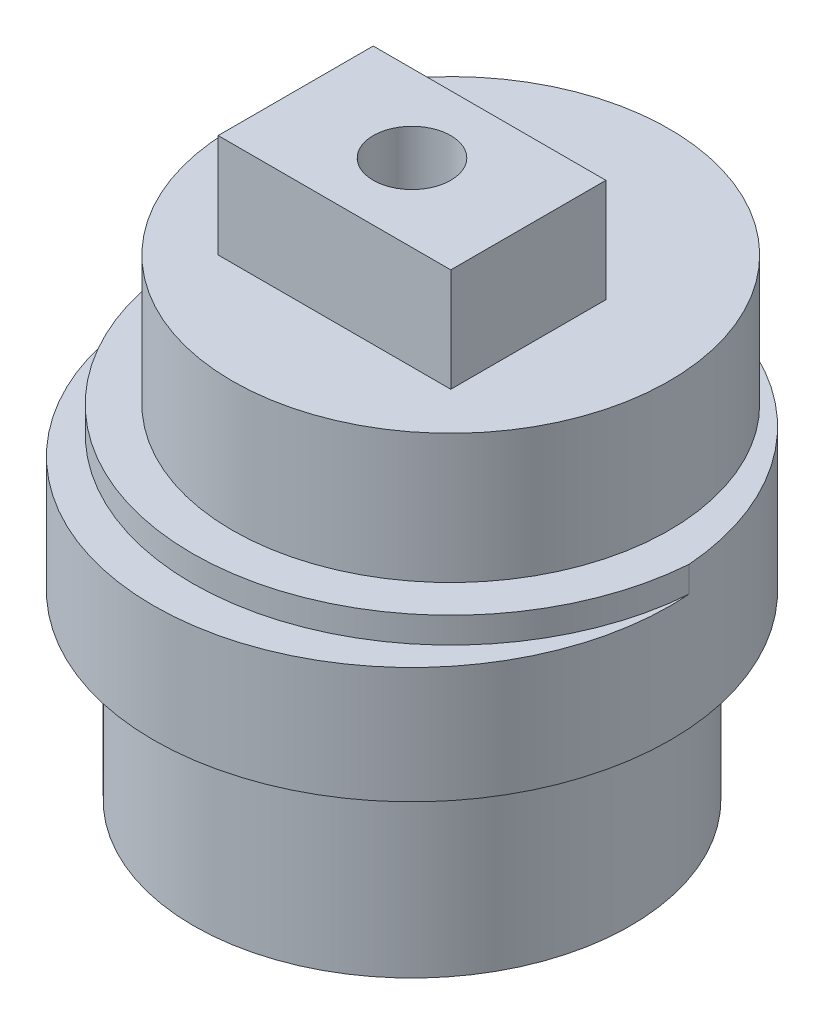
SolidWorks part; units mm, degrees
ref_plane "Front Plane" through (0, 0, 0) normal (0, 0, 1) x (1, 0, 0)
ref_plane "Top Plane" through (0, 0, 0) normal (0, 1, 0) x (1, 0, 0)
ref_plane "Right Plane" through (0, 0, 0) normal (1, 0, 0) x (0, 0, -1)
sketch "Sketch1" plane through (0, 0, 0) normal (0, 1, 0) x (1, 0, 0)
  circle A0 centre (0, 0) radius 8.45
  dimension "D1" = 16.9
extrude "Boss-Extrude1" add sketch "Sketch1" along normal blind 7
sketch "Sketch2" plane through (0, 7, 0) normal (0, 1, 0) x (1, 0, 0)
  circle A0 centre (0, 0) radius 10
  dimension "D1" = 20
extrude "Boss-Extrude2" add sketch "Sketch2" along normal blind 4.5
sketch "Sketch3" plane through (0, 11.5, 0) normal (0, 1, 0) x (1, 0, 0)
  circle A0 centre (0, 1.5) radius 8.45
  dimension "D1" = 16.9
  dimension "D2" = 1.5
extrude "Boss-Extrude3" add sketch "Sketch3" along normal blind 6
sketch "Sketch4" plane through (0, 11.5, 0) normal (0, 1, 0) x (1, 0, 0)
  circle A0 centre (0, 1.5) radius 8.45 construction
  circle A1 centre (0, 1.5) radius 8.45
  circle A2 centre (0, 0) radius 10 construction
  arc A3 (0, -10) -> (-9.9718, 0.75) centre (0, 0) ccw
  arc A4 (-9.9718, 0.75) -> (9.9718, 0.75) centre (0, 1.5) ccw
  arc A5 (9.9718, 0.75) -> (0, -10) centre (0, 0) ccw
  circle M1 centre (0, 1.5) radius 8.45
  circle M2 centre (0, 0) radius 10
  dimension "D1" = 20
extrude "Boss-Extrude4" add sketch "Sketch4" along normal blind 1 contours A4 M2 M1
sketch "Sketch5" plane through (0, 17.5, 0) normal (0, 1, 0) x (1, 0, 0)
  line L1 (-4.5, -3) -> (4.5, -3)
  line L2 (-4.5, -3) -> (-4.5, 3)
  line L3 (-4.5, 3) -> (4.5, 3)
  line L4 (4.5, -3) -> (4.5, 3)
  line L5 (-4.5, -3) -> (4.5, 3) construction
  line L6 (-4.5, 3) -> (4.5, -3) construction
  point P2 (0, 0)
  dimension "D3" = 9
  dimension "D4" = 6
extrude "Boss-Extrude5" add sketch "Sketch5" along normal blind 4
sketch "Sketch6" plane through (0, 21.5, 0) normal (0, 1, 0) x (1, 0, 0)
  circle A0 centre (0, 0) radius 1.5
  dimension "D1" = 3
extrude "Cut-Extrude1" cut sketch "Sketch6" against normal blind 8
sketch "Sketch7" plane through (0, 0, 0) normal (0, -1, 0) x (-1, 0, 0)
  circle A0 centre (0, -5.5) radius 1.5
  circle A1 centre (-5.5, 0) radius 1.5
  circle A2 centre (0, 5.5) radius 1.5
  circle A3 centre (5.5, 0) radius 1.5
  point P12 (0, 0)
  dimension "D3" = 3
  dimension "D1" = 5.5
  dimension "D2" = 4
extrude "Cut-Extrude2" [suppressed] cut sketch "Sketch7" against normal blind 8
sketch "Sketch8" plane through (0, 0, 0) normal (0, -1, 0) x (1, 0, 0)
  arc A0 (1.9433, 2.9259) -> (1.4435, 3.2021) centre (0, 0) ccw
  arc A1 (-2.4201, 2.5457) -> (-2.8006, 2.1199) centre (0, 0) ccw
  arc A2 (3.4992, 0.3049) -> (3.4036, 0.8679) centre (0, 0) ccw
  arc A3 (2.4201, -2.5457) -> (2.8006, -2.1199) centre (0, 0) ccw
  arc A4 (-1.0759, 3.3436) -> (-1.6035, 3.1251) centre (0, 0) ccw
  arc A5 (-3.0204, -1.793) -> (-2.6899, -2.2587) centre (0, 0) ccw
  arc A6 (0.4814, 3.4793) -> (-0.0888, 3.5113) centre (0, 0) ccw
  arc A7 (3.0204, 1.793) -> (2.6899, 2.2587) centre (0, 0) ccw
  arc A8 (3.285, -1.2435) -> (3.4431, -0.6948) centre (0, 0) ccw
  arc A9 (-3.285, 1.2435) -> (-3.4431, 0.6948) centre (0, 0) ccw
  arc A10 (1.0759, -3.3436) -> (1.6035, -3.1251) centre (0, 0) ccw
  arc A11 (-1.9433, -2.9259) -> (-1.4435, -3.2021) centre (0, 0) ccw
  arc A12 (-0.4814, -3.4793) -> (0.0888, -3.5113) centre (0, 0) ccw
  arc A13 (-3.4992, -0.3049) -> (-3.4036, -0.8679) centre (0, 0) ccw
  spline S0 degree 3 poles (-2.6899, -2.2587) (-2.6998, -2.278) (-2.7192, -2.3185) (-2.7467, -2.3829) (-2.7734, -2.4537) (-2.7988, -2.5314) (-2.8225, -2.6162) (-2.8438, -2.7079) (-2.8627, -2.8065) (-2.877, -2.9191) (-2.8909, -3.0073) (-2.8865, -3.0684) (-2.8815, -3.0926) (-2.874, -3.1162) (-2.8635, -3.1386) (-2.8488, -3.1646) (-2.8257, -3.1852) (-2.7982, -3.1969) (-2.7748, -3.2048) (-2.7506, -3.2097) (-2.7259, -3.2119) (-2.6647, -3.2094) (-2.5786, -3.1858) (-2.4684, -3.1589) (-2.3725, -3.1291) (-2.2837, -3.0977) (-2.2021, -3.0646) (-2.1277, -3.0307) (-2.0604, -2.9963) (-1.9994, -2.9617) (-1.9614, -2.9379) (-1.9433, -2.9259) knots 0.027203 0.027203 0.027203 0.027203 0.059318 0.093556 0.130845 0.171187 0.214581 0.261026 0.310525 0.363075 0.429245 0.441417 0.453589 0.465761 0.477933 0.490104 0.509896 0.522067 0.534239 0.546411 0.558583 0.570755 0.636925 0.689475 0.738974 0.785419 0.828813 0.869155 0.906444 0.940682 0.972797 0.972797 0.972797 0.972797 weights 1 1 1 1 1 1 1 1 1 1 1 1 1 1 1 1 1 1 1 1 1 1 1 1 1 1 1 1 1 1 1 1
  spline S1 degree 3 poles (-1.6035, 3.1251) (-1.6202, 3.139) (-1.6552, 3.1669) (-1.7119, 3.2081) (-1.775, 3.2498) (-1.8451, 3.2919) (-1.9225, 3.3339) (-2.0072, 3.3751) (-2.0992, 3.4154) (-2.2057, 3.4545) (-2.2886, 3.4876) (-2.3492, 3.4969) (-2.3739, 3.4975) (-2.3985, 3.4953) (-2.4227, 3.4901) (-2.4514, 3.4815) (-2.4765, 3.4637) (-2.4941, 3.4395) (-2.507, 3.4184) (-2.5172, 3.3958) (-2.5248, 3.3723) (-2.536, 3.312) (-2.5321, 3.2229) (-2.5304, 3.1094) (-2.5227, 3.0093) (-2.5119, 2.9157) (-2.4978, 2.8289) (-2.4812, 2.7487) (-2.4627, 2.6754) (-2.4425, 2.6083) (-2.4278, 2.566) (-2.4201, 2.5457) knots 0.027203 0.027203 0.027203 0.027203 0.059318 0.093556 0.130845 0.171187 0.214581 0.261026 0.310525 0.363075 0.429245 0.441417 0.453589 0.465761 0.477933 0.490104 0.509896 0.522067 0.534239 0.546411 0.558583 0.570755 0.636925 0.689475 0.738974 0.785419 0.828813 0.869155 0.906444 0.940682 0.972797 0.972797 0.972797 0.972797 weights 1 1 1 1 1 1 1 1 1 1 1 1 1 1 1 1 1 1 1 1 1 1 1 1 1 1 1 1 1 1 1 1
  spline S2 degree 3 poles (2.6899, 2.2587) (2.6998, 2.278) (2.7192, 2.3185) (2.7467, 2.3829) (2.7734, 2.4537) (2.7988, 2.5314) (2.8225, 2.6162) (2.8438, 2.7079) (2.8627, 2.8065) (2.877, 2.9191) (2.8909, 3.0073) (2.8865, 3.0684) (2.8815, 3.0926) (2.874, 3.1162) (2.8635, 3.1386) (2.8488, 3.1646) (2.8257, 3.1852) (2.7982, 3.1969) (2.7748, 3.2048) (2.7506, 3.2097) (2.7259, 3.2119) (2.6647, 3.2094) (2.5786, 3.1858) (2.4684, 3.1589) (2.3725, 3.1291) (2.2837, 3.0977) (2.2021, 3.0646) (2.1277, 3.0307) (2.0604, 2.9963) (1.9994, 2.9617) (1.9614, 2.9379) (1.9433, 2.9259) knots 0.027203 0.027203 0.027203 0.027203 0.059318 0.093556 0.130845 0.171187 0.214581 0.261026 0.310525 0.363075 0.429245 0.441417 0.453589 0.465761 0.477933 0.490104 0.509896 0.522067 0.534239 0.546411 0.558583 0.570755 0.636925 0.689475 0.738974 0.785419 0.828813 0.869155 0.906444 0.940682 0.972797 0.972797 0.972797 0.972797 weights 1 1 1 1 1 1 1 1 1 1 1 1 1 1 1 1 1 1 1 1 1 1 1 1 1 1 1 1 1 1 1 1
  spline S3 degree 3 poles (3.4036, 0.8679) (3.4208, 0.881) (3.4559, 0.909) (3.5086, 0.9551) (3.5633, 1.0074) (3.62, 1.0664) (3.6781, 1.1324) (3.7371, 1.2058) (3.7969, 1.2865) (3.8587, 1.3817) (3.9094, 1.4551) (3.9319, 1.5121) (3.938, 1.5361) (3.9414, 1.5606) (3.9417, 1.5853) (3.9397, 1.6152) (3.9279, 1.6437) (3.9082, 1.6662) (3.8905, 1.6835) (3.8708, 1.6984) (3.8495, 1.7111) (3.7933, 1.7354) (3.7055, 1.7515) (3.5945, 1.7751) (3.4952, 1.7899) (3.4016, 1.8001) (3.3137, 1.8057) (3.232, 1.8073) (3.1564, 1.8056) (3.0865, 1.8009) (3.0419, 1.7959) (3.0204, 1.793) knots 0.027203 0.027203 0.027203 0.027203 0.059318 0.093556 0.130845 0.171187 0.214581 0.261026 0.310525 0.363075 0.429245 0.441417 0.453589 0.465761 0.477933 0.490104 0.509896 0.522067 0.534239 0.546411 0.558583 0.570755 0.636925 0.689475 0.738974 0.785419 0.828813 0.869155 0.906444 0.940682 0.972797 0.972797 0.972797 0.972797 weights 1 1 1 1 1 1 1 1 1 1 1 1 1 1 1 1 1 1 1 1 1 1 1 1 1 1 1 1 1 1 1 1
  spline S4 degree 3 poles (2.8006, -2.1199) (2.8217, -2.1252) (2.8654, -2.1351) (2.9343, -2.1476) (3.0093, -2.1578) (3.0907, -2.1653) (3.1786, -2.1696) (3.2728, -2.1699) (3.3732, -2.1664) (3.4861, -2.1553) (3.5751, -2.1492) (3.6338, -2.1313) (3.6563, -2.1211) (3.6776, -2.1085) (3.6971, -2.0933) (3.7192, -2.0731) (3.7341, -2.0461) (3.7394, -2.0167) (3.7419, -1.9921) (3.7413, -1.9674) (3.7379, -1.9429) (3.7219, -1.8837) (3.6797, -1.8051) (3.629, -1.7036) (3.5786, -1.6167) (3.5282, -1.5371) (3.4778, -1.465) (3.4281, -1.4) (3.3796, -1.342) (3.3324, -1.2903) (3.3007, -1.2585) (3.285, -1.2435) knots 0.027203 0.027203 0.027203 0.027203 0.059318 0.093556 0.130845 0.171187 0.214581 0.261026 0.310525 0.363075 0.429245 0.441417 0.453589 0.465761 0.477933 0.490104 0.509896 0.522067 0.534239 0.546411 0.558583 0.570755 0.636925 0.689475 0.738974 0.785419 0.828813 0.869155 0.906444 0.940682 0.972797 0.972797 0.972797 0.972797 weights 1 1 1 1 1 1 1 1 1 1 1 1 1 1 1 1 1 1 1 1 1 1 1 1 1 1 1 1 1 1 1 1
  spline S5 degree 3 poles (-2.8006, 2.1199) (-2.8217, 2.1252) (-2.8654, 2.1351) (-2.9343, 2.1476) (-3.0093, 2.1578) (-3.0907, 2.1653) (-3.1786, 2.1696) (-3.2728, 2.1699) (-3.3732, 2.1664) (-3.4861, 2.1553) (-3.5751, 2.1492) (-3.6338, 2.1313) (-3.6563, 2.1211) (-3.6776, 2.1085) (-3.6971, 2.0933) (-3.7192, 2.0731) (-3.7341, 2.0461) (-3.7394, 2.0167) (-3.7419, 1.9921) (-3.7413, 1.9674) (-3.7379, 1.9429) (-3.7219, 1.8837) (-3.6797, 1.8051) (-3.629, 1.7036) (-3.5786, 1.6167) (-3.5282, 1.5371) (-3.4778, 1.465) (-3.4281, 1.4) (-3.3796, 1.342) (-3.3324, 1.2903) (-3.3007, 1.2585) (-3.285, 1.2435) knots 0.027203 0.027203 0.027203 0.027203 0.059318 0.093556 0.130845 0.171187 0.214581 0.261026 0.310525 0.363075 0.429245 0.441417 0.453589 0.465761 0.477933 0.490104 0.509896 0.522067 0.534239 0.546411 0.558583 0.570755 0.636925 0.689475 0.738974 0.785419 0.828813 0.869155 0.906444 0.940682 0.972797 0.972797 0.972797 0.972797 weights 1 1 1 1 1 1 1 1 1 1 1 1 1 1 1 1 1 1 1 1 1 1 1 1 1 1 1 1 1 1 1 1
  spline S6 degree 3 poles (1.4435, 3.2021) (1.444, 3.2238) (1.444, 3.2687) (1.4408, 3.3387) (1.4341, 3.414) (1.4233, 3.4951) (1.4079, 3.5817) (1.3873, 3.6736) (1.3615, 3.7707) (1.3256, 3.8783) (1.2998, 3.9638) (1.2693, 4.0169) (1.2543, 4.0366) (1.2373, 4.0546) (1.2182, 4.0702) (1.1936, 4.0872) (1.1639, 4.0958) (1.134, 4.0944) (1.1095, 4.0914) (1.0855, 4.0852) (1.0624, 4.0765) (1.0083, 4.0478) (0.941, 3.9891) (0.8533, 3.9171) (0.7798, 3.8486) (0.7135, 3.7818) (0.6543, 3.7166) (0.6021, 3.6537) (0.5563, 3.5935) (0.5164, 3.5359) (0.4925, 3.498) (0.4814, 3.4793) knots 0.027203 0.027203 0.027203 0.027203 0.059318 0.093556 0.130845 0.171187 0.214581 0.261026 0.310525 0.363075 0.429245 0.441417 0.453589 0.465761 0.477933 0.490104 0.509896 0.522067 0.534239 0.546411 0.558583 0.570755 0.636925 0.689475 0.738974 0.785419 0.828813 0.869155 0.906444 0.940682 0.972797 0.972797 0.972797 0.972797 weights 1 1 1 1 1 1 1 1 1 1 1 1 1 1 1 1 1 1 1 1 1 1 1 1 1 1 1 1 1 1 1 1
  spline S7 degree 3 poles (-1.4435, -3.2021) (-1.444, -3.2238) (-1.444, -3.2687) (-1.4408, -3.3387) (-1.4341, -3.414) (-1.4233, -3.4951) (-1.4079, -3.5817) (-1.3873, -3.6736) (-1.3615, -3.7707) (-1.3256, -3.8783) (-1.2998, -3.9638) (-1.2693, -4.0169) (-1.2543, -4.0366) (-1.2373, -4.0546) (-1.2182, -4.0702) (-1.1936, -4.0872) (-1.1639, -4.0958) (-1.134, -4.0944) (-1.1095, -4.0914) (-1.0855, -4.0852) (-1.0624, -4.0765) (-1.0083, -4.0478) (-0.941, -3.9891) (-0.8533, -3.9171) (-0.7798, -3.8486) (-0.7135, -3.7818) (-0.6543, -3.7166) (-0.6021, -3.6537) (-0.5563, -3.5935) (-0.5164, -3.5359) (-0.4925, -3.498) (-0.4814, -3.4793) knots 0.027203 0.027203 0.027203 0.027203 0.059318 0.093556 0.130845 0.171187 0.214581 0.261026 0.310525 0.363075 0.429245 0.441417 0.453589 0.465761 0.477933 0.490104 0.509896 0.522067 0.534239 0.546411 0.558583 0.570755 0.636925 0.689475 0.738974 0.785419 0.828813 0.869155 0.906444 0.940682 0.972797 0.972797 0.972797 0.972797 weights 1 1 1 1 1 1 1 1 1 1 1 1 1 1 1 1 1 1 1 1 1 1 1 1 1 1 1 1 1 1 1 1
  spline S8 degree 3 poles (-3.4036, -0.8679) (-3.4208, -0.881) (-3.4559, -0.909) (-3.5086, -0.9551) (-3.5633, -1.0074) (-3.62, -1.0664) (-3.6781, -1.1324) (-3.7371, -1.2058) (-3.7969, -1.2865) (-3.8587, -1.3817) (-3.9094, -1.4551) (-3.9319, -1.5121) (-3.938, -1.5361) (-3.9414, -1.5606) (-3.9417, -1.5853) (-3.9397, -1.6152) (-3.9279, -1.6437) (-3.9082, -1.6662) (-3.8905, -1.6835) (-3.8708, -1.6984) (-3.8495, -1.7111) (-3.7933, -1.7354) (-3.7055, -1.7515) (-3.5945, -1.7751) (-3.4952, -1.7899) (-3.4016, -1.8001) (-3.3137, -1.8057) (-3.232, -1.8073) (-3.1564, -1.8056) (-3.0865, -1.8009) (-3.0419, -1.7959) (-3.0204, -1.793) knots 0.027203 0.027203 0.027203 0.027203 0.059318 0.093556 0.130845 0.171187 0.214581 0.261026 0.310525 0.363075 0.429245 0.441417 0.453589 0.465761 0.477933 0.490104 0.509896 0.522067 0.534239 0.546411 0.558583 0.570755 0.636925 0.689475 0.738974 0.785419 0.828813 0.869155 0.906444 0.940682 0.972797 0.972797 0.972797 0.972797 weights 1 1 1 1 1 1 1 1 1 1 1 1 1 1 1 1 1 1 1 1 1 1 1 1 1 1 1 1 1 1 1 1
  spline S9 degree 3 poles (3.4431, -0.6948) (3.4643, -0.6905) (3.508, -0.6804) (3.5756, -0.6618) (3.6475, -0.6385) (3.7242, -0.6099) (3.8052, -0.5756) (3.8902, -0.535) (3.9791, -0.4883) (4.0761, -0.4293) (4.1536, -0.3852) (4.1987, -0.3436) (4.2145, -0.3246) (4.2282, -0.304) (4.2392, -0.2819) (4.2504, -0.2541) (4.2521, -0.2233) (4.2441, -0.1945) (4.2357, -0.1713) (4.2244, -0.1493) (4.2107, -0.1286) (4.1706, -0.0823) (4.0985, -0.0298) (4.0087, 0.0397) (3.9256, 0.0961) (3.8457, 0.1459) (3.769, 0.1891) (3.6961, 0.2261) (3.6272, 0.2573) (3.5622, 0.2834) (3.5199, 0.2982) (3.4992, 0.3049) knots 0.027203 0.027203 0.027203 0.027203 0.059318 0.093556 0.130845 0.171187 0.214581 0.261026 0.310525 0.363075 0.429245 0.441417 0.453589 0.465761 0.477933 0.490104 0.509896 0.522067 0.534239 0.546411 0.558583 0.570755 0.636925 0.689475 0.738974 0.785419 0.828813 0.869155 0.906444 0.940682 0.972797 0.972797 0.972797 0.972797 weights 1 1 1 1 1 1 1 1 1 1 1 1 1 1 1 1 1 1 1 1 1 1 1 1 1 1 1 1 1 1 1 1
  spline S10 degree 3 poles (-0.0888, 3.5113) (-0.0977, 3.5311) (-0.1172, 3.5715) (-0.1505, 3.6332) (-0.1892, 3.6981) (-0.2341, 3.7665) (-0.2856, 3.8379) (-0.344, 3.9117) (-0.4094, 3.988) (-0.4885, 4.0694) (-0.5487, 4.1352) (-0.5993, 4.1698) (-0.6213, 4.1811) (-0.6444, 4.1899) (-0.6685, 4.1957) (-0.698, 4.2003) (-0.7284, 4.1952) (-0.7548, 4.181) (-0.7755, 4.1676) (-0.7945, 4.1517) (-0.8116, 4.1338) (-0.8478, 4.0844) (-0.883, 4.0024) (-0.9307, 3.8994) (-0.9672, 3.8058) (-0.998, 3.7168) (-1.023, 3.6325) (-1.0429, 3.5531) (-1.058, 3.479) (-1.0689, 3.4098) (-1.074, 3.3652) (-1.0759, 3.3436) knots 0.027203 0.027203 0.027203 0.027203 0.059318 0.093556 0.130845 0.171187 0.214581 0.261026 0.310525 0.363075 0.429245 0.441417 0.453589 0.465761 0.477933 0.490104 0.509896 0.522067 0.534239 0.546411 0.558583 0.570755 0.636925 0.689475 0.738974 0.785419 0.828813 0.869155 0.906444 0.940682 0.972797 0.972797 0.972797 0.972797 weights 1 1 1 1 1 1 1 1 1 1 1 1 1 1 1 1 1 1 1 1 1 1 1 1 1 1 1 1 1 1 1 1
  spline S11 degree 3 poles (1.6035, -3.1251) (1.6202, -3.139) (1.6552, -3.1669) (1.7119, -3.2081) (1.775, -3.2498) (1.8451, -3.2919) (1.9225, -3.3339) (2.0072, -3.3751) (2.0992, -3.4154) (2.2057, -3.4545) (2.2886, -3.4876) (2.3492, -3.4969) (2.3739, -3.4975) (2.3985, -3.4953) (2.4227, -3.4901) (2.4514, -3.4815) (2.4765, -3.4637) (2.4941, -3.4395) (2.507, -3.4184) (2.5172, -3.3958) (2.5248, -3.3723) (2.536, -3.312) (2.5321, -3.2229) (2.5304, -3.1094) (2.5227, -3.0093) (2.5119, -2.9157) (2.4978, -2.8289) (2.4812, -2.7487) (2.4627, -2.6754) (2.4425, -2.6083) (2.4278, -2.566) (2.4201, -2.5457) knots 0.027203 0.027203 0.027203 0.027203 0.059318 0.093556 0.130845 0.171187 0.214581 0.261026 0.310525 0.363075 0.429245 0.441417 0.453589 0.465761 0.477933 0.490104 0.509896 0.522067 0.534239 0.546411 0.558583 0.570755 0.636925 0.689475 0.738974 0.785419 0.828813 0.869155 0.906444 0.940682 0.972797 0.972797 0.972797 0.972797 weights 1 1 1 1 1 1 1 1 1 1 1 1 1 1 1 1 1 1 1 1 1 1 1 1 1 1 1 1 1 1 1 1
  spline S12 degree 3 poles (-3.4431, 0.6948) (-3.4643, 0.6905) (-3.508, 0.6804) (-3.5756, 0.6618) (-3.6475, 0.6385) (-3.7242, 0.6099) (-3.8052, 0.5756) (-3.8902, 0.535) (-3.9791, 0.4883) (-4.0761, 0.4293) (-4.1536, 0.3852) (-4.1987, 0.3436) (-4.2145, 0.3246) (-4.2282, 0.304) (-4.2392, 0.2819) (-4.2504, 0.2541) (-4.2521, 0.2233) (-4.2441, 0.1945) (-4.2357, 0.1713) (-4.2244, 0.1493) (-4.2107, 0.1286) (-4.1706, 0.0823) (-4.0985, 0.0298) (-4.0087, -0.0397) (-3.9256, -0.0961) (-3.8457, -0.1459) (-3.769, -0.1891) (-3.6961, -0.2261) (-3.6272, -0.2573) (-3.5622, -0.2834) (-3.5199, -0.2982) (-3.4992, -0.3049) knots 0.027203 0.027203 0.027203 0.027203 0.059318 0.093556 0.130845 0.171187 0.214581 0.261026 0.310525 0.363075 0.429245 0.441417 0.453589 0.465761 0.477933 0.490104 0.509896 0.522067 0.534239 0.546411 0.558583 0.570755 0.636925 0.689475 0.738974 0.785419 0.828813 0.869155 0.906444 0.940682 0.972797 0.972797 0.972797 0.972797 weights 1 1 1 1 1 1 1 1 1 1 1 1 1 1 1 1 1 1 1 1 1 1 1 1 1 1 1 1 1 1 1 1
  spline S13 degree 3 poles (0.0888, -3.5113) (0.0977, -3.5311) (0.1172, -3.5715) (0.1505, -3.6332) (0.1892, -3.6981) (0.2341, -3.7665) (0.2856, -3.8379) (0.344, -3.9117) (0.4094, -3.988) (0.4885, -4.0694) (0.5487, -4.1352) (0.5993, -4.1698) (0.6213, -4.1811) (0.6444, -4.1899) (0.6685, -4.1957) (0.698, -4.2003) (0.7284, -4.1952) (0.7548, -4.181) (0.7755, -4.1676) (0.7945, -4.1517) (0.8116, -4.1338) (0.8478, -4.0844) (0.883, -4.0024) (0.9307, -3.8994) (0.9672, -3.8058) (0.998, -3.7168) (1.023, -3.6325) (1.0429, -3.5531) (1.058, -3.479) (1.0689, -3.4098) (1.074, -3.3652) (1.0759, -3.3436) knots 0.027203 0.027203 0.027203 0.027203 0.059318 0.093556 0.130845 0.171187 0.214581 0.261026 0.310525 0.363075 0.429245 0.441417 0.453589 0.465761 0.477933 0.490104 0.509896 0.522067 0.534239 0.546411 0.558583 0.570755 0.636925 0.689475 0.738974 0.785419 0.828813 0.869155 0.906444 0.940682 0.972797 0.972797 0.972797 0.972797 weights 1 1 1 1 1 1 1 1 1 1 1 1 1 1 1 1 1 1 1 1 1 1 1 1 1 1 1 1 1 1 1 1
extrude "Cut-Extrude3" cut sketch "Sketch8" against normal blind 16
